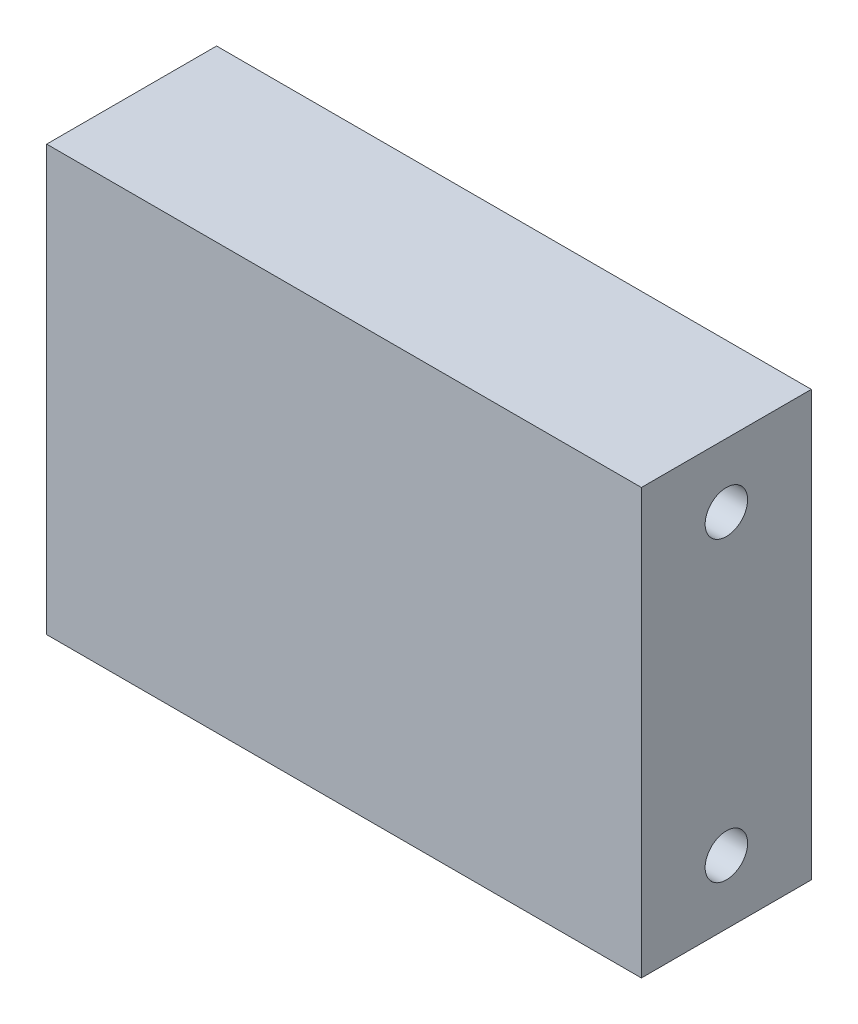
SolidWorks part; units mm, degrees
ref_plane "Front Plane" through (0, 0, 0) normal (0, 0, 1) x (1, 0, 0)
ref_plane "Top Plane" through (0, 0, 0) normal (0, 1, 0) x (1, 0, 0)
ref_plane "Right Plane" through (0, 0, 0) normal (1, 0, 0) x (0, 0, -1)
sketch "Sketch1" plane through (0, 0, 0) normal (0, 1, 0) x (1, 0, 0)
  line L1 (0, 0) -> (177.8, 0)
  line L2 (0, 0) -> (0, 50.8)
  line L3 (0, 50.8) -> (177.8, 50.8)
  line L4 (177.8, 0) -> (177.8, 50.8)
  dimension "D1" = 50.8
  dimension "D2" = 177.8
extrude "Boss-Extrude1" add sketch "Sketch1" along normal blind 127
sketch "Sketch2" plane through (177.8, 0, 0) normal (1, 0, 0) x (0, 0, -1)
sketch "Sketch3" plane through (0, 0, 0) normal (-1, 0, 0) x (0, 0, 1)
  line L0 (-25.4, 127) -> (-25.4, 0) construction
  line L1 (-50.8, 127) -> (0, 127) construction
  line L2 (-50.8, 0) -> (0, 0) construction
  line L3 (0, 63.5) -> (-50.8, 63.5) construction
  line L4 (0, 127) -> (0, 0) construction
  line L5 (-50.8, 127) -> (-50.8, 0) construction
  circle A1 centre (-25.4, 19.05) radius 6.35
  circle A2 centre (-25.4, 107.95) radius 6.35
  dimension "D1" = 88.9
  dimension "D2" = 12.7
extrude "Cut-Extrude1" cut sketch "Sketch3" against normal through all
